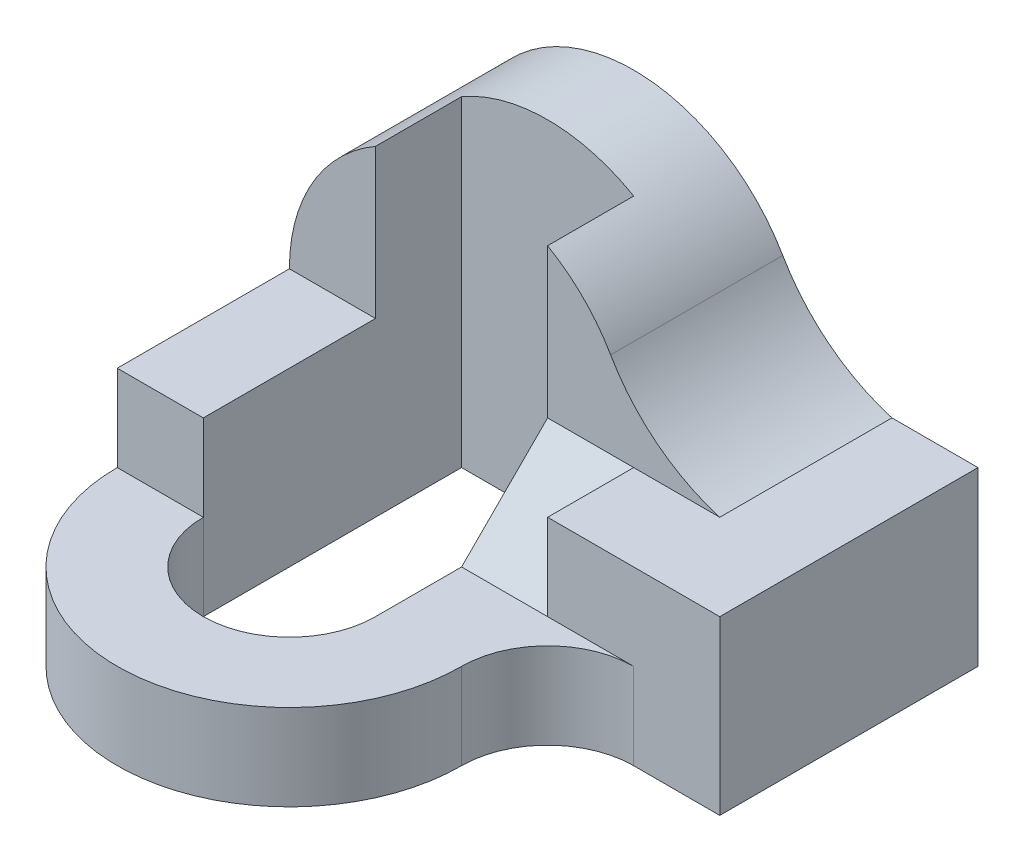
SolidWorks part; units mm, degrees
ref_plane "Front Plane" through (0, 0, 0) normal (0, 0, 1) x (1, 0, 0)
ref_plane "Top Plane" through (0, 0, 0) normal (0, 1, 0) x (1, 0, 0)
ref_plane "Right Plane" through (0, 0, 0) normal (1, 0, 0) x (0, 0, -1)
sketch "Sketch1" plane through (0, 0, 0) normal (0, 0, 1) x (1, 0, 0)
  line L1 (3, -1) -> (-3, -1)
  line L2 (3, -1) -> (3, 1)
  line L3 (3, 1) -> (-3, 1)
  line L4 (-3, -1) -> (-3, 1)
  line L5 (3, -1) -> (-3, 1) construction
  line L6 (3, 1) -> (-3, -1) construction
  point P0 (0, 0)
  dimension "D1" = 6
  dimension "D2" = 2
extrude "Boss-Extrude2" add sketch "Sketch1" along normal blind 3
sketch "Sketch3" plane through (0, 0, 0) normal (0, 0, -1) x (-1, 0, 0)
  line L0 (-3, 1) -> (3, 1) construction
  line L1 (-2, 1) -> (3, 1)
  arc A0 (3, 1) -> (-0.7321, 2) centre (1, 1) ccw
  arc A1 (-0.7321, 2) -> (-2, 1) centre (-2.62, 3.09) cw
  point P0 (1, 1)
  dimension "D1" = 2
  dimension "D2" = 1
  dimension "D3" = 1
extrude "Boss-Extrude3" add sketch "Sketch3" against normal blind 2
sketch "Sketch4" plane through (0, 0, 3) normal (0, 0, 1) x (1, 0, 0)
  line L0 (-3, -1) -> (3, -1) construction
  line L1 (0, -1) -> (0, 2.7321)
  line L2 (-2, -1) -> (-2, 2.7321)
  line L3 (-3, 1) -> (-3, -1) construction
  line L5 (3, -1) -> (3, 1) construction
  line L6 (0, -1) -> (-2, -1)
  arc A0 (0.7321, 2) -> (-3, 1) centre (-1, 1) ccw construction
  arc A1 (0, 2.7321) -> (-2, 2.7321) centre (-1, 1) ccw
  dimension "D1" = 1
  dimension "D3" = 3
extrude "Cut-Extrude2" cut sketch "Sketch4" against normal blind 2
sketch "Sketch5" plane through (0, 0, 0) normal (-1, 0, 0) x (0, 0, 1)
  line L0 (2, 1) -> (3, 0)
  line L1 (3, -1) -> (3, 1) construction
  line L2 (3, 0) -> (3, 1)
  line L3 (3, 1) -> (2, 1)
  dimension "D1" = 1
extrude "Cut-Extrude3" cut sketch "Sketch5" against normal blind 1
sketch "Sketch6" plane through (0, 1, 0) normal (0, 1, 0) x (1, 0, 0)
  line L0 (0, -1) -> (-2, -1)
  line L1 (-2, -3) -> (-2, -4)
  line L2 (0, -3) -> (0, -4)
  line L3 (-3, -4) -> (-3, -3)
  line L4 (3, -3) -> (1, -3) construction
  line L5 (2, -3) -> (0, -3)
  line L6 (-3, -3) -> (-3, -2) construction
  line L7 (-2, -3) -> (-3, -3)
  arc A0 (0, -4) -> (-2, -4) centre (-1, -4) cw
  arc A1 (-3, -4) -> (1, -4) centre (-1, -4) ccw
  arc A2 (1, -4) -> (2, -3) centre (2, -4) cw
  line M1 (-3, -3) -> (-2, -3)
  dimension "D3" = 2
  dimension "D4" = 1
  dimension "D1" = 3
  dimension "D2" = 3
  dimension "D5" = 1
extrude "Boss-Extrude5" add sketch "Sketch6" against normal blind 2 contours A1 A2 L5 L2 A0 L1 L3 M1
sketch "Sketch7" plane through (0, 1, 0) normal (0, 1, 0) x (1, 0, 0)
  line L0 (-2, -4) -> (-3, -4)
  line L1 (2, -3) -> (0, -3)
  line L2 (0, -3) -> (0, -4)
  arc A0 (-3, -4) -> (1, -4) centre (-1, -4) ccw construction
  arc A1 (0, -4) -> (-2, -4) centre (-1, -4) cw
  arc A2 (-3, -4) -> (1, -4) centre (-1, -4) ccw
  arc A3 (1, -4) -> (2, -3) centre (2, -4) cw
extrude "Cut-Extrude4" cut sketch "Sketch7" against normal blind 1
